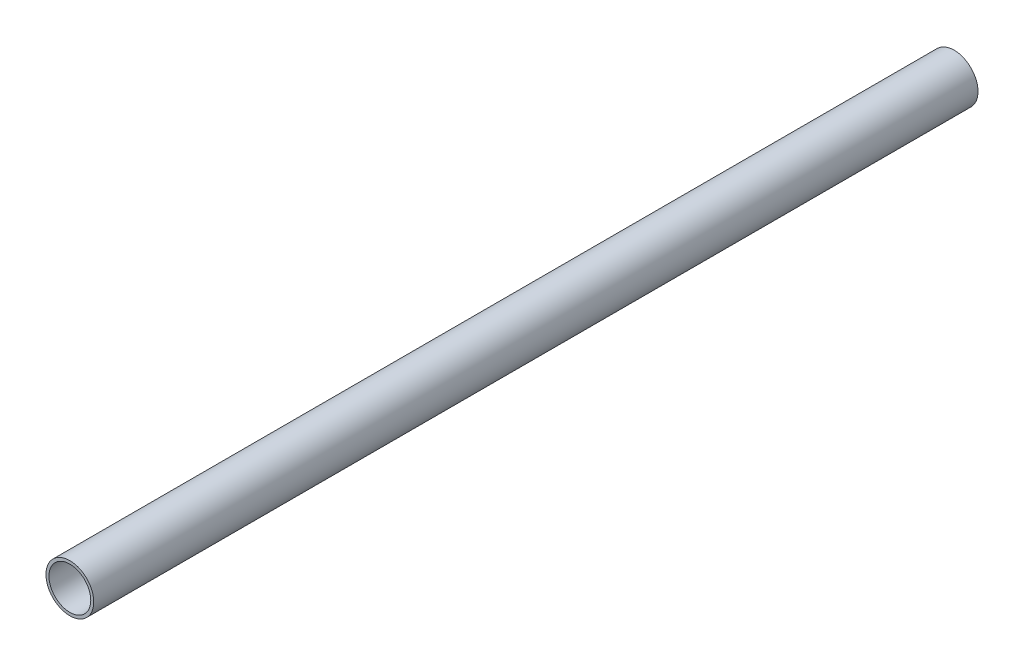
SolidWorks part; units mm, degrees
material "PVC Rigid"
ref_plane "Front Plane" through (0, 0, 0) normal (0, 0, 1) x (1, 0, 0)
ref_plane "Top Plane" through (0, 0, 0) normal (0, 1, 0) x (1, 0, 0)
ref_plane "Right Plane" through (0, 0, 0) normal (1, 0, 0) x (0, 0, -1)
sketch "Sketch1" plane through (0, 0, 0) normal (0, 0, 1) x (1, 0, 0)
  circle A0 centre (0, 0) radius 12.7
  circle A1 centre (0, 0) radius 11.1125
  dimension "D1" = 25.4
  dimension "D2" = 22.225
extrude "Boss-Extrude1" add sketch "Sketch1" along normal blind 469.9
